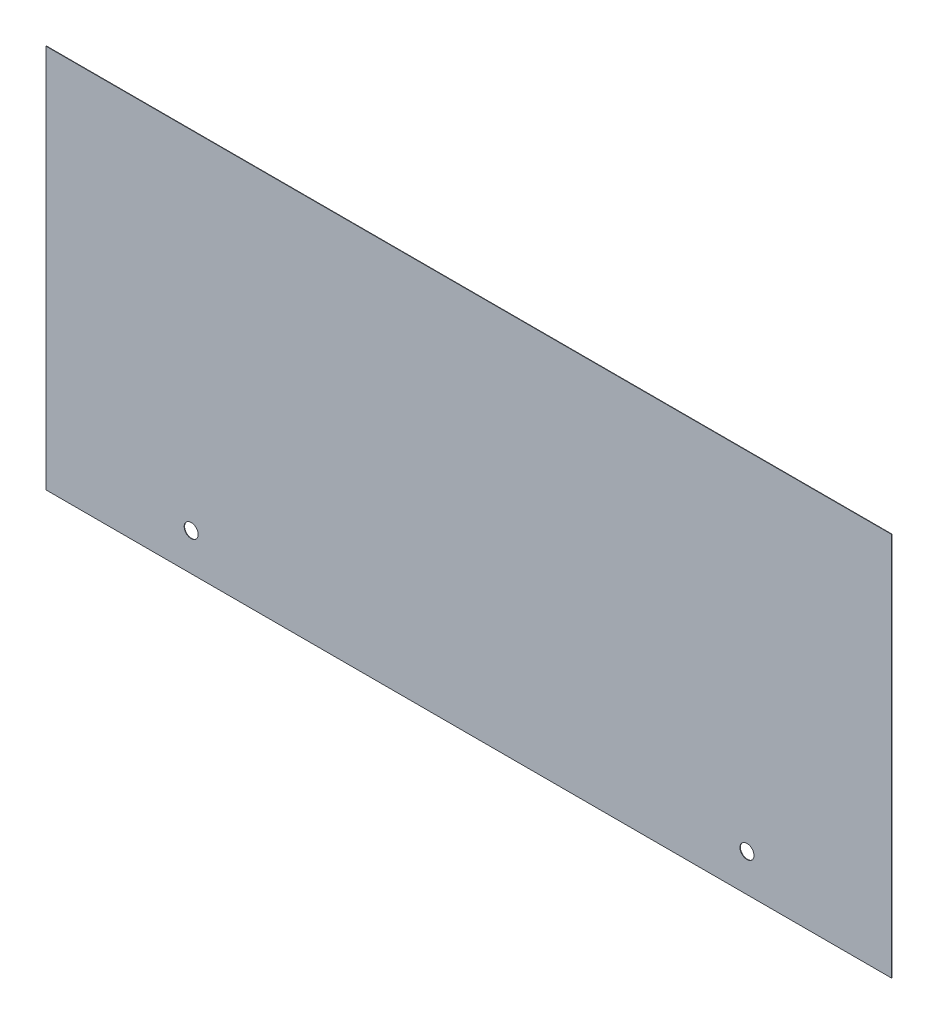
SolidWorks part; units mm, degrees
material "Acrylic (Medium-high impact)"
ref_plane "Front Plane" through (0, 0, 0) normal (0, 0, 1) x (1, 0, 0)
ref_plane "Top Plane" through (0, 0, 0) normal (0, 1, 0) x (1, 0, 0)
ref_plane "Right Plane" through (0, 0, 0) normal (1, 0, 0) x (0, 0, -1)
sketch "Sketch1" plane through (0, 0, 0) normal (0, 0, 1) x (1, 0, 0)
  line L0 (-251.3838, 405.0538) -> (-251.3838, 408.1272) construction
  line L1 (251.3838, -405.0538) -> (-251.3838, -405.0538)
  line L2 (251.3838, -405.0538) -> (251.3838, 405.0538)
  line L3 (251.3838, 405.0538) -> (-251.3838, 405.0538)
  line L4 (-251.3838, -405.0538) -> (-251.3838, 405.0538)
  line L5 (251.3838, -405.0538) -> (-251.3838, 405.0538) construction
  line L6 (251.3838, 405.0538) -> (-251.3838, -405.0538) construction
  point P0 (0, 0)
  dimension "D1" = 502.7676
  dimension "D2" = 3.0734
  dimension "D3" = 813.181
extrude "Boss-Extrude1" add sketch "Sketch1" along normal blind 0.254
sketch "Sketch2" plane through (0, 0, 0) normal (0, 0, -1) x (-1, 0, 0)
  line L0 (-165.481, 395.1478) -> (165.1254, 395.1478) construction
  line L1 (165.1254, 395.1478) -> (165.1254, -382.8288) construction
  line L2 (165.1254, -382.8288) -> (-165.481, -382.8288) construction
  line L3 (-165.481, -382.8288) -> (-165.481, 395.1478) construction
  line L4 (-251.3838, -405.0538) -> (-251.3838, 405.0538) construction
  line L5 (-251.3838, 405.0538) -> (251.3838, 405.0538) construction
  line L6 (251.3838, -405.0538) -> (-251.3838, -405.0538) construction
  circle A0 centre (-165.481, 395.1478) radius 4.1656
  circle A1 centre (165.1254, 395.1478) radius 4.1656
  circle A2 centre (165.1254, -382.8288) radius 4.1656
  circle A3 centre (-165.481, -382.8288) radius 4.1656
  dimension "D1" = 8.3312
  dimension "D2" = 85.9028
  dimension "D3" = 9.906
  dimension "D4" = 330.6064
  dimension "D5" = 22.225
extrude "Cut-Extrude1" cut sketch "Sketch2" against normal through all
sketch "Sketch3" plane through (0, 0, 0.254) normal (0, 0, 1) x (1, 0, 0)
  line L0 (251.3838, -405.0538) -> (251.3838, 405.0538) construction
  line L1 (-251.3838, 405.0538) -> (251.3838, 405.0538)
  line L2 (-251.3838, 405.0538) -> (-251.3838, -176.4538)
  line L3 (-251.3838, -176.4538) -> (251.3838, -176.4538)
  line L4 (251.3838, 405.0538) -> (251.3838, -176.4538)
  line L5 (-251.3838, -405.0538) -> (251.3838, -405.0538) construction
  dimension "D1" = 228.6
extrude "Cut-Extrude2" cut sketch "Sketch3" against normal through all
equation "\"Height\"= 32in"
equation "\"Width\"= 23in"
equation "\"Depth\"= 20in"
equation "\"Plexi\"= .121in"
equation "\"EBWidth\" = 9in"
equation "\"MagnetThickness\"= 0.125in"
equation "\"MagnetDiameter\"= 12mm"
equation "\"DoorPlexi\" = \"Plexi\""
equation "\"BasePlateThickness\" = 0.5in"
equation "\"BasePlateWidth\" = \"Width\"+\"EBWidth\"-2*\"Plexi\""
equation "\"BasePlateDepth\" = \"TopBarDepth\"+2*\"CornerCube\""
equation "\"Boxsize\" = .75in"
equation "\"BoxsizeHalf\" = \"Boxsize\"/2"
equation "\"Boxinner\" = .625in"
equation "\"CornerCube\" = 0.75in"
equation "\"FingerLength\" = 1.125in"
equation "\"FingerWidth\" = .625in"
equation "\"Cutwidth\"= .016in"
equation "\"Earsize\"= 1in + \"Cutwidth\" /2"
equation "\"Slotsize\" = 1in - \"CutWidth\" / 2"
equation "\"InnerWidth\" = \"Width\" - 2* \"Plexi\""
equation "\"InnerHeight\" = \"Height\" -2 * \"Plexi\""
equation "\"InnerDepth\" = \"Depth\" - 2*\"Plexi\""
equation "\"FrontDoorGap\" = .1in"
equation "\"TopDepth\" = \"Depth\"-\"DoorPlexi\"-\"FrontDoorGap\""
equation "\"TopBarDepth\" = \"Depth\"-\"DoorPlexi\"-\"Plexi\"-2*\"MagnetThickness\"-2*\"CornerCube\""
equation "\"RearNumHoles\" = 4"
equation "\"RearHolesBorder\" = 2.25"
equation "\"RearHoleSpacing\" = (\"Width\" - 2*\"RearHolesBorder\") / (\"RearNumHoles\"-1)"
equation "\"RearBarLength\" = (\"InnerWidth\"-2*\"CornerCube\")"
equation "\"RearTopNumHoles\" = 4"
equation "\"RearTopHolesBorder\" = 3.1"
equation "\"RearTopHolesSpacing\" = (\"Width\" - 2*\"RearTopHolesBorder\") / (\"RearTopNumHoles\"-1)"
equation "\"SideTopNumHoles\" = 4"
equation "\"SideTopHoleOffset\"=\"CornerCube\"+\"FingerLength\"+\"Plexi\"+.5"
equation "\"SideTopHoleSpacing\" = (\"TopBarDepth\"-2*\"SideTopHoleOffset\") / (\"SideTopNumHoles\"-1)"
equation "\"SideHorizNumHoles\" = 4"
equation "\"SideHorizHoleBorder\" = 1.50"
equation "\"SideHorizHoleSpacing\" = (\"TopBarDepth\"-2*\"SideHorizHoleBorder\") / (\"SideHorizNumHoles\"-1)"
equation "\"SideVertBarLength\"=\"Height\"-\"BasePlateThickness\"-2*\"CornerCube\"-\"Plexi\""
equation "\"SideVertNumHoles\" = 4"
equation "\"SideVertHolesBorder\" = \"CornerCube\"+\"FingerLength\"+1.50"
equation "\"SideVertHoleSpacing\" = (\"InnerHeight\" - 2*\"SideVertHolesBorder\") / (\"SideVertNumHoles\"-1)"
equation "\"RearSideVertNumHoles\" = 4"
equation "\"RearSideVertHolesBorder\" = 2.4"
equation "\"RearSideVertHoleSpacing\" = (\"InnerHeight\" - 2*\"RearSideVertHolesBorder\") / (\"RearSideVertNumHoles\"-1)"
equation "\"RivetDia\" = .228in"
equation "\"SlotDepth\" = \"Plexi\" + 0.75in + .005in"
equation "\"SideSlotWidth\"   = \"Plexi\"+.005in"
equation "\"SidePanelVertSpacing\" = (\"Height\"-2*(1.75-\"Plexi\")) / 5"
equation "\"BottomPanelSideHoleSpacing\" = (\"InnerDepth\"-2*(1.75-\"Plexi\")) / 4"
equation "\"CoolerDepth\" = 12in"
equation "\"ShelfGap\" = 0.5in"
equation "\"ShelfDepth\" = \"TopBarDepth\"+\"CornerCube\"-\"CoolerDepth\""
equation "\"ShelfBarDepth\"=\"ShelfDepth\"-2*\"CornerCube\""
equation "\"ShelfWidth\" = \"EBWidth\"-\"ShelfGap\""
equation "\"ShelfBarWidth\" = \"EBWidth\"-\"Boxsize\""
equation "\"ShelfBarWidthShort\" = \"ShelfBarWidth\"-\"Boxsize\"-\"ShelfGap\""
equation "\"IntakeWidth\"=4in"
equation "\"IntakeHeight\"=2in"
equation "\"ExhaustWidth\"=4in"
equation "\"ExhaustHeight\"=2in"
equation "\"VentSpacing\"=7in"
equation "\"AngleBracketLength\"=20mm"
equation "\"AngleBracketWidth\"=.5in"
equation "\"AngleBracketThickness\"=.125in"
equation "\"AngleBracketHolePos\"=15mm"
equation "\"AngleBracketHoleDia\"=\"Rivet3_16Dia\""
equation "\"ShelfBarAngleHole\"=\"ShelfGap\"+\"Boxsize\"+\"AngleBracketHolePosShort\""
equation "\"D1@Sketch1\"=\"TopDepth\"+\"RivNutHeight\""
equation "\"D2@Sketch1\"=\"Plexi\""
equation "\"D3@Sketch1\"=\"Height\"+\"RivNutHeight\""
equation "\"D1@Boss-Extrude1\"=\"Plexi\""
equation "\"ComponentMountDia\"=0.1770"
equation "\"ShelfThickness\" = .1250in"
equation "\"Rivet3_16Dia\" = .191in"
equation "\"BinderPostDia\" = .228in"
equation "\"ShelfHeight1\" = 13in"
equation "\"ShelfHeight2\" = 24in"
equation "\"VentVertLocation\"=12.75in"
equation "\"AngleBracketLengthShort\"=.625in"
equation "\"AngleBracketLengthLong\"=1in"
equation "\"AngleBracketHolePosShort\"=.358in"
equation "\"AngleBracketHolePosLong\"=.7in"
equation "\"PSBracketThickness\" = .0641in"
equation "\"EBForwardMountOffset\" = 4.0in"
equation "\"EBForwardMount\" = 2*\"Boxsize\"+\"CoolerDepth\"+\"EBForwardMountOffset\""
equation "\"EBRearwardMountOffset\" = 1.5in"
equation "\"EBRearwardMount\"= \"Boxsize\"+\"EBRearwardMountOffset\""
equation "\"MagSealWidth\" = \"InnerWidth\""
equation "\"MagSealHeight\" = \"Height\"-\"BasePlateThickness\"-\"Plexi\""
equation "\"MagWidth\" = .500in"
equation "\"SiliconeSealOD\" = .3125in"
equation "\"SiliconeSealID\" = .1875in"
equation "\"SiliconeSealWidth\" = \"MagSealWidth\" - 2*\"MagWidth\"-\"SiliconeSealOD\""
equation "\"SiliconeSealHeigth\" = \"MagSealHeight\" - 2*\"MagWidth\"-\"SiliconeSealOD\""
equation "\"HooknLoopThick\" = .085in"
equation "\"HooknLoopWidth\" = 0.75in"
equation "\"HooknLoopHeigth\" = 0.75in"
equation "\"RivNutHeight\" = 0.015in"
equation "\"D2@Sketch2\"=\"Plexi\"+\"RivNutHeight\"+\"CornerCube\"+\"SideTopHoleOffset\""
equation "\"D3@Sketch2\"=\"RivNutHeight\"+\"BoxsizeHalf\""
equation "\"D4@Sketch2\"=\"SideTopHoleSpacing\"*3"
equation "\"D5@Sketch2\"=\"BasePlateThickness\"+\"BoxsizeHalf\""
equation "\"D1@Sketch2\"=\"RivetDia\"+.1"
